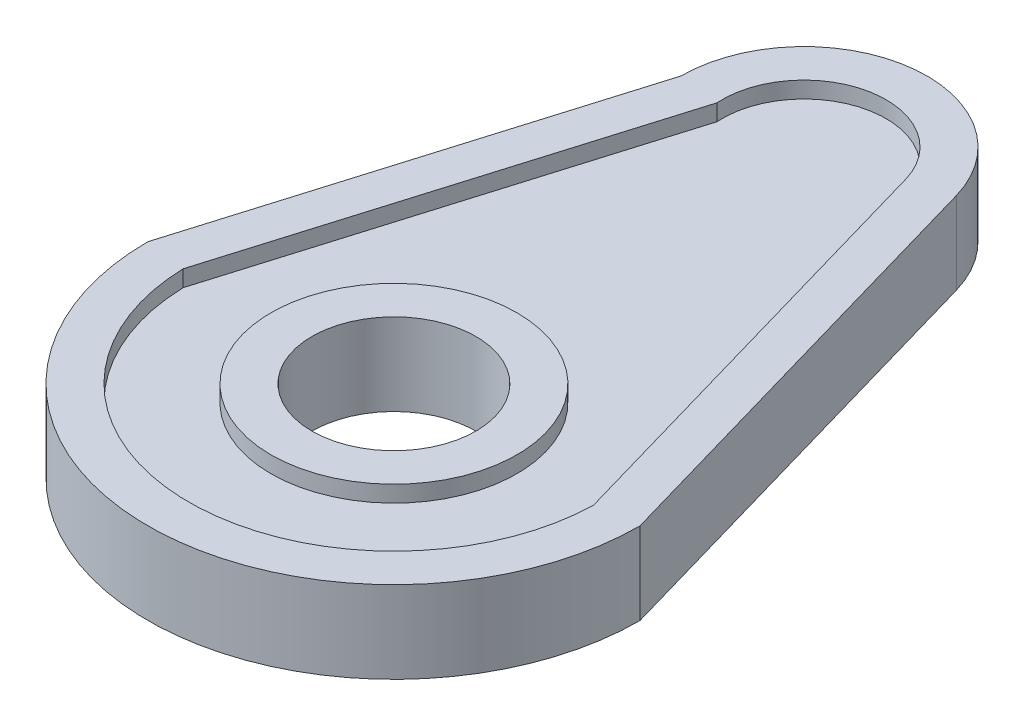
SolidWorks part; units mm, degrees
ref_plane "Front Plane" through (0, 0, 0) normal (0, 0, 1) x (1, 0, 0)
ref_plane "Top Plane" through (0, 0, 0) normal (0, 1, 0) x (1, 0, 0)
ref_plane "Right Plane" through (0, 0, 0) normal (1, 0, 0) x (0, 0, -1)
sketch "Sketch1" plane through (0, 0, 0) normal (0, 1, 0) x (1, 0, 0)
  line L0 (0, 50) -> (0, 0) construction
  line L1 (-15, 50) -> (-30, 0)
  line L2 (14.4148, 54.1489) -> (30, 0)
  circle A0 centre (0, 0) radius 30
  circle A1 centre (0, 50) radius 15
  dimension "D1" = 30
  dimension "D2" = 60
  dimension "D3" = 50
extrude "Boss-Extrude1" add sketch "Sketch1" along normal mid plane 10
sketch "Sketch2" plane through (0, 5, 0) normal (0, 1, 0) x (1, 0, 0)
  line L4 (24.9909, -0.6737) -> (9.6099, 52.7659)
  line L5 (-9.9781, 49.339) -> (-24.9902, -0.7011)
  line L6 (24.9909, -0.6737) -> (9.6099, 52.7659)
  line L7 (-9.9781, 49.339) -> (-24.9902, -0.7011)
  arc A4 (9.6099, 52.7659) -> (-9.9781, 49.339) centre (0, 50) ccw
  arc A5 (-24.9902, -0.7011) -> (24.9909, -0.6737) centre (0, 0) ccw
  arc A6 (9.6099, 52.7659) -> (-9.9781, 49.339) centre (0, 50) ccw
  arc A7 (-24.9902, -0.7011) -> (24.9909, -0.6737) centre (0, 0) ccw
  dimension "D1" = 5
extrude "Cut-Extrude1" cut sketch "Sketch2" against normal blind 2
mirror "Mirror1" about plane through (0, 0, 0) normal (0, 1, 0) of "Cut-Extrude1"
sketch "Sketch3" plane through (0, 3, 0) normal (0, 1, 0) x (1, 0, 0)
  circle A0 centre (0, 0) radius 10
  dimension "D1" = 20
extrude "Cut-Extrude2" cut sketch "Sketch3" against normal through all
sketch "Sketch4" plane through (0, 3, 0) normal (0, 1, 0) x (1, 0, 0)
  circle A0 centre (0, 0) radius 10 construction
  circle A1 centre (0, 0) radius 10
  circle A2 centre (0, 0) radius 15
  dimension "D1" = 30
extrude "Boss-Extrude2" add sketch "Sketch4" along normal blind 2
mirror "Mirror2" about plane through (0, 0, 0) normal (0, 1, 0) of "Boss-Extrude2"
